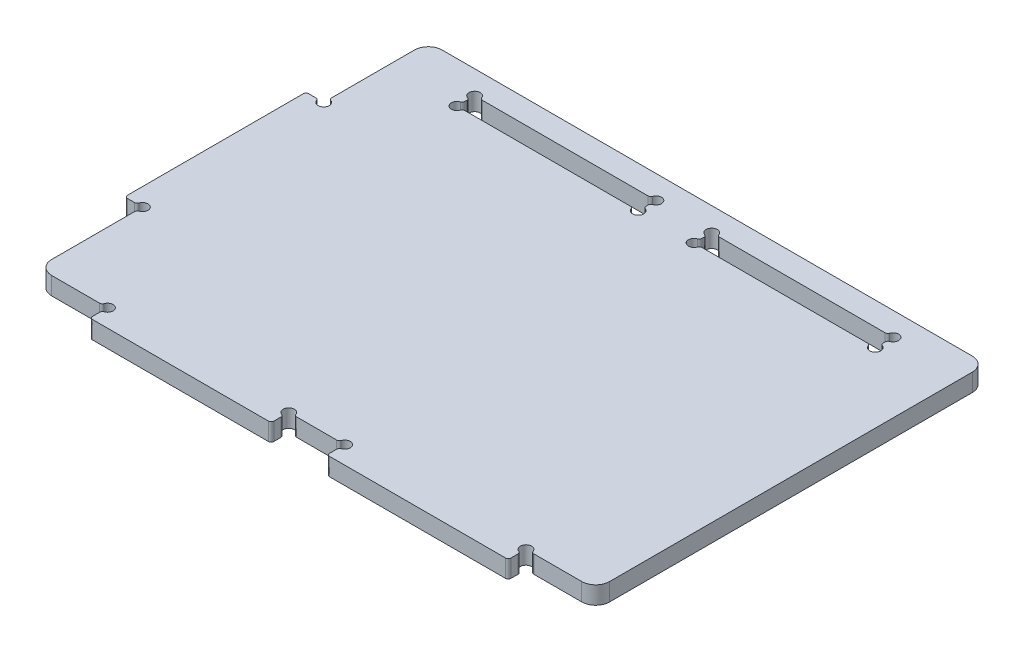
SolidWorks part; units mm, degrees
material "Maple"
ref_plane "Front Plane" through (0, 0, 0) normal (0, 0, 1) x (1, 0, 0)
ref_plane "Top Plane" through (0, 0, 0) normal (0, 1, 0) x (1, 0, 0)
ref_plane "Right Plane" through (0, 0, 0) normal (1, 0, 0) x (0, 0, -1)
sketch "Sketch1" plane through (0, 0, 0) normal (0, 1, 0) x (1, 0, 0)
  line L1 (-100, 70) -> (100, 70)
  line L2 (-100, 70) -> (-100, -70)
  line L3 (-100, -70) -> (100, -70)
  line L4 (100, 70) -> (100, -70)
  line L5 (-100, 70) -> (100, -70) construction
  line L6 (-100, -70) -> (100, 70) construction
  point P0 (0, 0)
  dimension "D1" = 200
  dimension "D2" = 140
extrude "Boss-Extrude1" add sketch "Sketch1" against normal blind 6.35
sketch "Sketch4" plane through (0, 0, 0) normal (0, 1, 0) x (1, 0, 0)
  line L0 (-100, -70) -> (100, -70) construction
  line L1 (-75, -70) -> (-10, -70)
  line L2 (-75, -70) -> (-75, -76.35)
  line L3 (-75, -76.35) -> (-10, -76.35)
  line L4 (-10, -70) -> (-10, -76.35)
  line L5 (-100, 70) -> (-100, -70) construction
  dimension "D1" = 6.35
  dimension "D2" = 25
  dimension "D3" = 65
extrude "Boss-Extrude2" add sketch "Sketch4" against normal up to surface (6.35 mm away) up to face at (0, -6.35, 0)
pattern_linear "LPattern1" count 2 spacing 85 along (1, 0, 0) of "Boss-Extrude2"
sketch "Sketch5" plane through (0, 0, 0) normal (0, 1, 0) x (1, 0, 0)
  line L0 (-100, 70) -> (-100, -70) construction
  line L1 (-100, 32.5) -> (-106.35, 32.5)
  line L2 (-100, 32.5) -> (-100, -32.5)
  line L3 (-100, -32.5) -> (-106.35, -32.5)
  line L4 (-106.35, 32.5) -> (-106.35, -32.5)
  line L7 (-100, 70) -> (-100, 32.5) construction
  line L8 (-100, -32.5) -> (-100, -70) construction
  dimension "D1" = 6.35
  dimension "D2" = 65
extrude "Boss-Extrude3" add sketch "Sketch5" against normal up to surface (6.35 mm away) up to face at (0, -6.35, 48.7833)
sketch "Sketch6" plane through (0, 0, 0) normal (0, 1, 0) x (1, 0, 0)
  line L1 (10, 61.6) -> (75, 61.6)
  line L2 (10, 61.6) -> (10, 55.25)
  line L3 (10, 55.25) -> (75, 55.25)
  line L4 (75, 61.6) -> (75, 55.25)
  line L5 (100, -70) -> (100, 70) construction
  line L6 (100, 70) -> (-100, 70) construction
  dimension "D1" = 14.75
  dimension "D2" = 65
  dimension "D3" = 6.35
  dimension "D4" = 25
extrude "Cut-Extrude3" cut sketch "Sketch6" against normal up to surface (6.35 mm away) up to face at (-25.7938, -6.35, 36.5875)
sketch "Sketch7" plane through (0, 0, 0) normal (0, 1, 0) x (1, 0, 0)
  circle A1 centre (10, 55.25) radius 2
  circle A3 centre (75, 55.25) radius 2
  circle A4 centre (10, 61.6) radius 2
  circle A5 centre (75, 61.6) radius 2
  dimension "D1" = 4
extrude "Cut-Extrude4" cut sketch "Sketch7" against normal up to surface (6.35 mm away) up to face at (42.5, -6.35, -58.425)
fillet "Fillet4" radius 1 8 edges at (73, -3.175, -55.25) (75, -3.175, -57.25) (12, -3.175, -55.25) (10, -3.175, -57.25) (75, -3.175, -59.6) (73, -3.175, -61.6) (12, -3.175, -61.6) (10, -3.175, -59.6)
pattern_linear "LPattern2" count 2 spacing 85 along (-1, 0, 0) of "Cut-Extrude3", "Cut-Extrude4", "Fillet4"
fillet "Fillet5" radius 5 4 edges at (-100, -3.175, 70) (100, -3.175, 70) (100, -3.175, -70) (-100, -3.175, -70)
sketch "Sketch8" plane through (0, 0, 0) normal (0, 1, 0) x (1, 0, 0)
  circle A0 centre (-75, -70) radius 2
  circle A1 centre (-10, -70) radius 2
  circle A2 centre (10, -70) radius 2
  circle A3 centre (75, -70) radius 2
  circle A4 centre (-100, 32.5) radius 2
  circle A5 centre (-100, -32.5) radius 2
  dimension "D1" = 4
extrude "Cut-Extrude6" cut sketch "Sketch8" against normal up to surface (6.35 mm away) up to face at (-42.5, -6.35, -58.425)
fillet "Fillet6" radius 1 18 edges at (77, -3.175, 70) (75, -3.175, 72) (75, -3.175, 76.35) (10, -3.175, 76.35) (10, -3.175, 72) (8, -3.175, 70) (-8, -3.175, 70) (-10, -3.175, 72) (-10, -3.175, 76.35) (-75, -3.175, 76.35) (-75, -3.175, 72) (-77, -3.175, 70) (-100, -3.175, 34.5) (-102, -3.175, 32.5) (-106.35, -3.175, 32.5) (-106.35, -3.175, -32.5) (-102, -3.175, -32.5) (-100, -3.175, -34.5)
